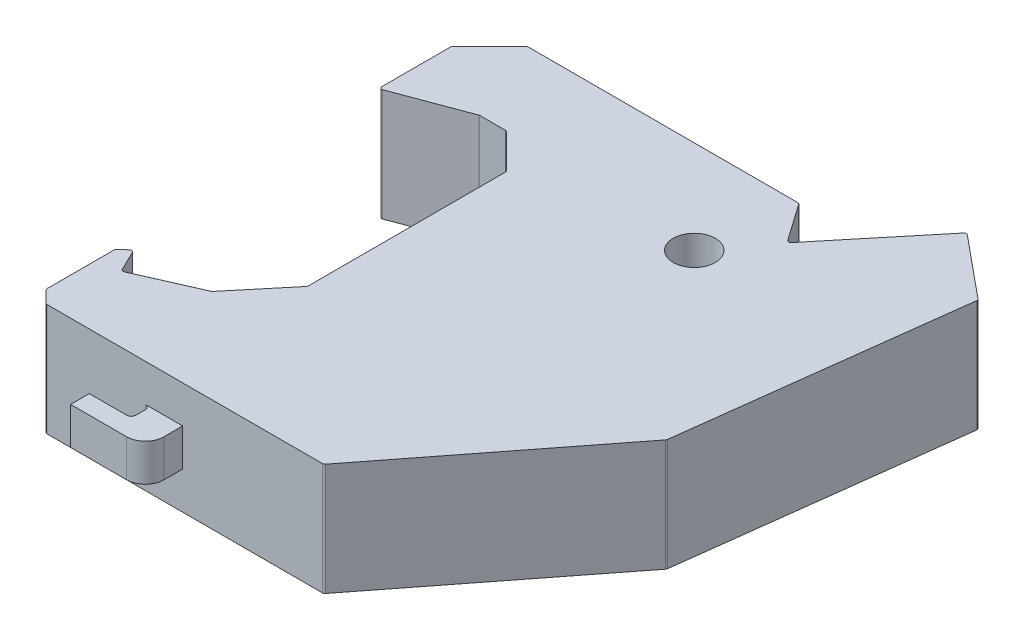
SolidWorks part; units mm, degrees
ref_plane "Front Plane" through (0, 0, 0) normal (0, 0, 1) x (1, 0, 0)
ref_plane "Top Plane" through (0, 0, 0) normal (0, 1, 0) x (1, 0, 0)
ref_plane "Right Plane" through (0, 0, 0) normal (1, 0, 0) x (0, 0, -1)
sketch "Sketch1" plane through (0, 0, 0) normal (0, 1, 0) x (1, 0, 0)
  line L0 (50.7574, 18.4002) -> (52.7574, 18.3985) construction
  line L18 (29.1219, 39.6749) -> (33.1219, 39.6749) construction
  line L19 (0, 0) -> (0, 8.7351)
  line L20 (0, 8.7351) -> (1.0535, 9.7222)
  line L21 (1.0535, 9.7222) -> (2.3456, 7.0723)
  line L23 (13.74, 15.6306) -> (13.74, 36.9341)
  line L24 (13.74, 36.9341) -> (9.9532, 40.7209)
  line L25 (9.9532, 40.7209) -> (7.0643, 40.7209)
  line L26 (7.0643, 40.7209) -> (-0.8094, 37.7834)
  line L27 (-0.8094, 37.7834) -> (-0.8094, 45.6047)
  line L28 (-0.8094, 45.6047) -> (3.2584, 49.6724)
  line L29 (3.2584, 49.6724) -> (32.3615, 49.6724)
  line L30 (32.3615, 49.6724) -> (35.3847, 45.3636)
  line L31 (35.3847, 45.3636) -> (44.0932, 55.9302)
  line L32 (44.0932, 55.9302) -> (50.9267, 50.2983)
  line L33 (50.9267, 50.2983) -> (47.2111, 20.6393)
  line L34 (47.2111, 20.6393) -> (31.1166, 0)
  line L35 (31.1166, 0) -> (0, 0)
  line L36 (13.74, 15.6306) -> (9.0909, 10.0427)
  line L37 (9.0909, 10.0427) -> (2.3456, 7.0723)
  circle A1 centre (31.1166, 39.6921) radius 2.25
  point P6 (44.5652, 55.7264)
  point P7 (0, 0)
  point P23 (0, 0)
  point P24 (0, 0)
  dimension "D2" = 4.5
  dimension "D1" = 4
extrude "Boss-Extrude1" add sketch "Sketch1" along normal blind 12
sketch "Sketch2" plane through (0, 0, 0) normal (0, 0, 1) x (1, 0, 0)
  line L0 (12, 0) -> (12, 12) construction
  line L1 (0, 0) -> (31.1166, 0) construction
  line L2 (0, 12) -> (31.1166, 12) construction
  line L4 (16, 8) -> (8, 8)
  line L5 (16, 8) -> (16, 4)
  line L6 (16, 4) -> (8, 4)
  line L7 (8, 8) -> (8, 4)
  line L8 (16, 8) -> (8, 4) construction
  line L9 (16, 4) -> (8, 8) construction
  point P6 (12, 6)
  dimension "D1" = 12
  dimension "D2" = 4
  dimension "D3" = 8
extrude "Boss-Extrude2" add sketch "Sketch2" along normal blind 4 contours L5 L4 L7 L6
sketch "Sketch3" plane through (0, 8, 0) normal (0, 1, 0) x (1, 0, 0)
  line L0 (12.5, -4) -> (12.5, 0) construction
  line L1 (16, -4) -> (8, -4) construction
  line L2 (0, 0) -> (31.1166, 0) construction
  line L4 (8, 0) -> (12, 0)
  line L5 (8, 0) -> (8, -2)
  line L6 (8, -2) -> (12, -2)
  line L7 (12.5, -0.5) -> (12.5, -1.5)
  line L9 (8, -4) -> (8, 0) construction
  line L14 (14, -4) -> (16, -4)
  line L15 (16, -4) -> (16, -2)
  arc A0 (12, -2) -> (12.5, -1.5) centre (12, -1.5) ccw
  arc A1 (12, 0) -> (12.5, -0.5) centre (12, -0.5) cw
  arc A2 (16, -2) -> (14, -4) centre (14, -2) cw
  point P13 (12.5, -2)
  point P30 (16, -4)
  dimension "D2" = 0.5
  dimension "D3" = 0.5
  dimension "D4" = 2
  dimension "D1" = 2
  dimension "D5" = 4
extrude "Cut-Extrude1" cut sketch "Sketch3" against normal blind 6
sketch "Sketch4" plane through (0, 12, 0) normal (0, 1, 0) x (1, 0, 0)
  line L0 (0, 0) -> (0, 1.364)
  line L1 (0, 8.7351) -> (0, 0) construction
  line L2 (0, 1.364) -> (1.364, 0)
  line L3 (0, 0) -> (31.1166, 0) construction
  line L4 (1.364, 0) -> (0, 0)
extrude "Cut-Extrude2" cut sketch "Sketch4" against normal through all
fillet "Fillet1" radius 0.25 19 edges at (-0.8094, 6, -37.7834) (-0.8094, 6, -45.6047) (3.2584, 6, -49.6724) (32.3615, 6, -49.6724) (35.3847, 6, -45.3636) (44.0932, 6, -55.9302) (50.9267, 6, -50.2983) (47.2111, 6, -20.6393) (31.1166, 6, 0) (7.0643, 6, -40.7209) (9.9532, 6, -40.7209) (13.74, 6, -36.9341) (13.74, 6, -15.6306) (9.0909, 6, -10.0427) (2.3456, 6, -7.0723) (1.0535, 6, -9.7222) (0, 6, -8.7351) (0, 6, -1.364) (1.364, 6, 0)
